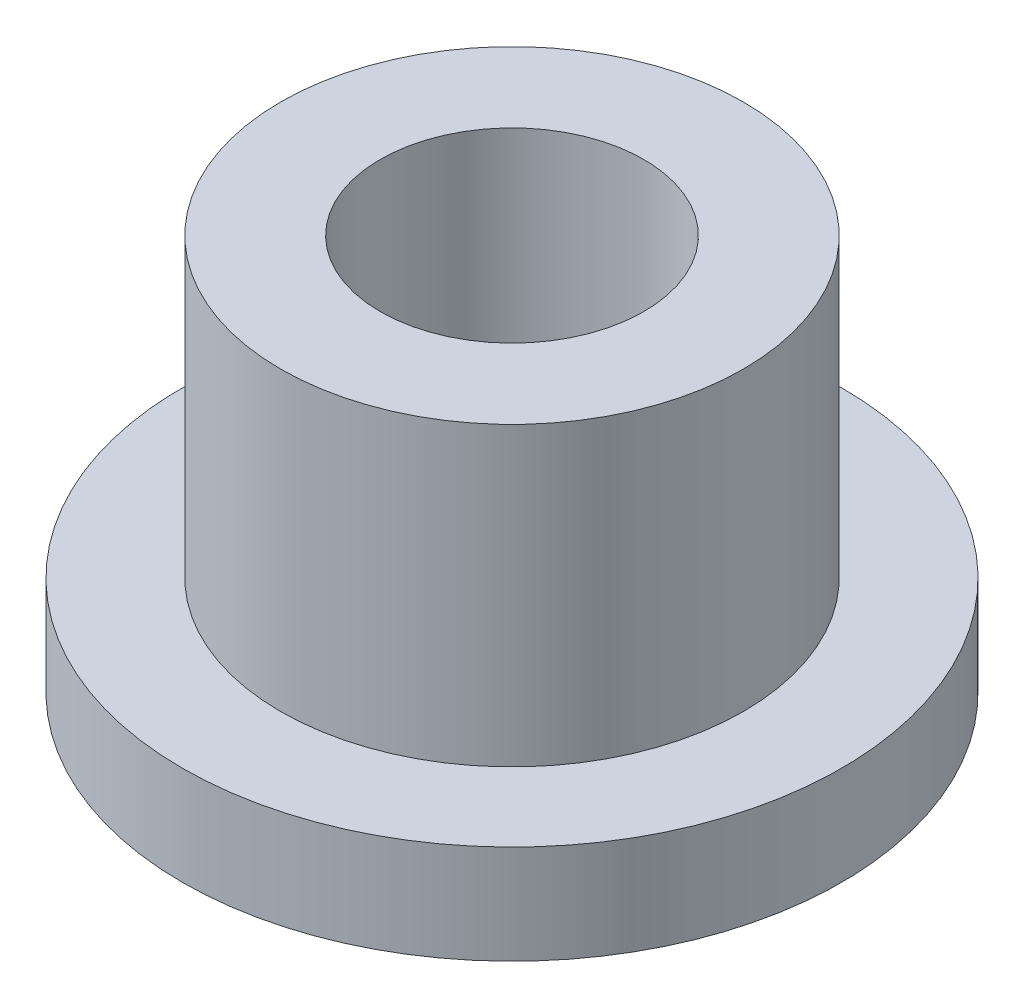
SolidWorks part; units mm, degrees
ref_plane "Front" through (0, 0, 0) normal (0, 0, 1) x (1, 0, 0)
ref_plane "Top" through (0, 0, 0) normal (0, 1, 0) x (1, 0, 0)
ref_plane "Right" through (0, 0, 0) normal (1, 0, 0) x (0, 0, -1)
sketch "Sketch1" plane through (0, 0, 0) normal (0, 1, 0) x (1, 0, 0)
  circle A0 centre (0, 0) radius 2
  circle A1 centre (0, 0) radius 3.51
  circle A2 centre (0, 0) radius 5
  dimension "ID" = 4
  dimension "OD" = 7.02
  dimension "FlangeOD" = 10
sketch "Sketch2" plane through (0, 0, 0) normal (0, 1, 0) x (1, 0, 0)
  circle A0 centre (0, 0) radius 2 construction
  circle A1 centre (0, 0) radius 3.51 construction
  circle A2 centre (0, 0) radius 2
  circle A3 centre (0, 0) radius 3.51
extrude "Boss-Extrude1" add sketch "Sketch2" along normal blind 6
sketch "Sketch3" plane through (0, 0, 0) normal (0, 1, 0) x (1, 0, 0)
  circle A0 centre (0, 0) radius 5 construction
  circle A1 centre (0, 0) radius 3.51 construction
  circle A2 centre (0, 0) radius 5
  circle A3 centre (0, 0) radius 3.51
extrude "Boss-Extrude2" add sketch "Sketch3" along normal blind 1.5
